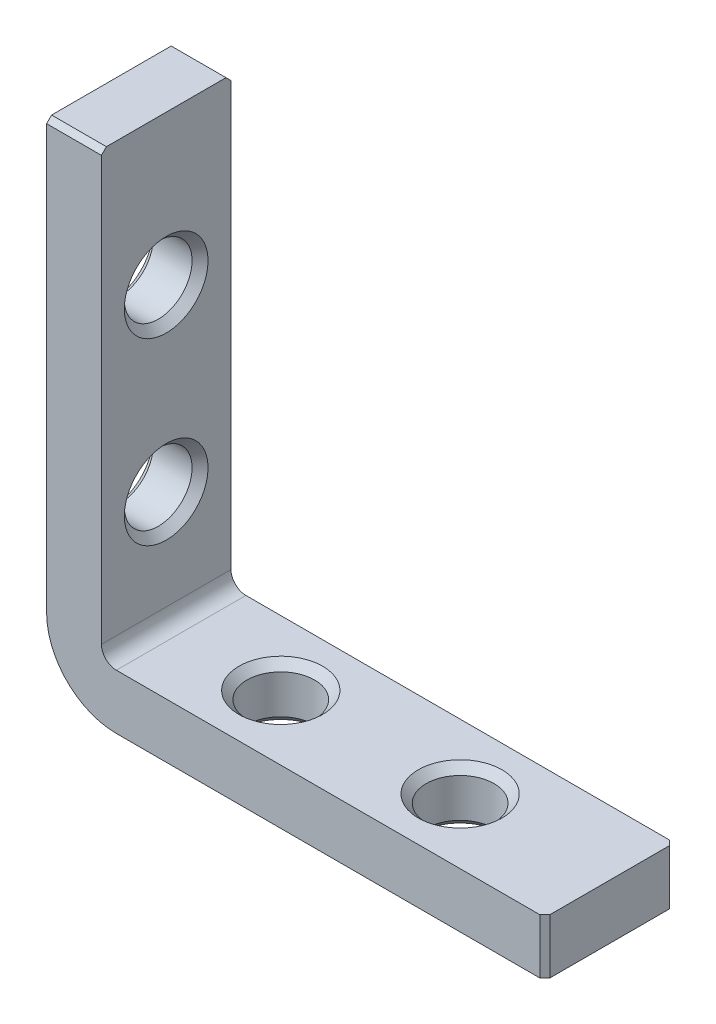
SolidWorks part; units mm, degrees
material "Сталь 20  ГОСТ 1050-2013"
ref_plane "Спереди" through (0, 0, 0) normal (0, 0, 1) x (1, 0, 0)
ref_plane "Сверху" through (0, 0, 0) normal (0, 1, 0) x (1, 0, 0)
ref_plane "Справа" through (0, 0, 0) normal (1, 0, 0) x (0, 0, -1)
sketch "Эскиз1" plane through (0, 0, 0) normal (0, 0, 1) x (1, 0, 0)
  line L0 (0, 50) -> (0, 7)
  line L1 (7, 0) -> (50, 0)
  line L2 (50, 5.5) -> (7, 5.5)
  line L3 (5.5, 7) -> (5.5, 50)
  line L8 (50, 5.5) -> (50, 0)
  line L9 (5.5, 50) -> (0, 50)
  arc A4 (0, 7) -> (7, 0) centre (7, 7) ccw
  arc A5 (7, 5.5) -> (5.5, 7) centre (7, 7) cw
  point P9 (0, 0)
  point P12 (0, 0)
  point P13 (5.5, 7)
  dimension "D3" = 7
  dimension "D1" = 50
  dimension "D2" = 5.5
extrude "Бобышка-Вытянуть1" add sketch "Эскиз1" along normal mid plane 13
hole_wizard "Отверстие обработанное метчиком M81" positions "Эскиз4" profile "Эскиз5" tap size "M8" standard "ISO" end condition through all
sketch "Эскиз4" plane through (0, 0, 0) normal (-1, 0, 0) x (0, 0, 1)
  line L9 (6.5, 50) -> (-6.5, 50) construction
  point P0 (0, 35)
  point P2 (0, 17)
  dimension "D1" = 15
  dimension "D2" = 18
sketch "Эскиз5" plane through (0, 35, 0) normal (0, 1, 0) x (0, 0, 1)
  line L0 (0, 0) -> (0, 5.5)
  line L1 (0, 5.5) -> (4.2, 5.5)
  line L2 (3.4, 4.7) -> (3.4, 0.8)
  line L3 (3.4, 0.8) -> (4.2, 0)
  line L5 (4.2, 0) -> (0, 0)
  line L6 (-3.4, 0.8) -> (-4.2, 0) construction
  line L7 (4.2, 5.5) -> (3.4, 4.7)
  line L8 (-4.2, 5.5) -> (-3.4, 4.7) construction
  line L11 (0, -6.35) -> (0, 107.95) construction
  dimension "Диаметр проходного сверла" = 6.8
  dimension "Глубина проходного сверла" = 5.5
  dimension "Диаметр передней зенковки" = 8.4
  dimension "Угол передней зенковки" = 90
  dimension "Диаметр задней зенковки" = 8.4
  dimension "Угол задней зенковки" = 90
cosmetic thread "Отверстие резьбы1" parameters "D2"=8
cosmetic thread "Отверстие резьбы2" parameters "D2"=8
ref_plane "Плоскость1" through (0, 0, 0) normal (-0.7071, 0.7071, 0) x (0.7071, 0.7071, 0)
mirror "Зеркальное отражение1" about plane through (0, 0, 0) normal (-0.7071, 0.7071, 0) of "Отверстие обработанное метчиком M81"
chamfer "Фаска1" distance 0.5 angle 45 4 edges at (50, 2.75, -6.5) (50, 2.75, 6.5) (2.75, 50, -6.5) (2.75, 50, 6.5)
